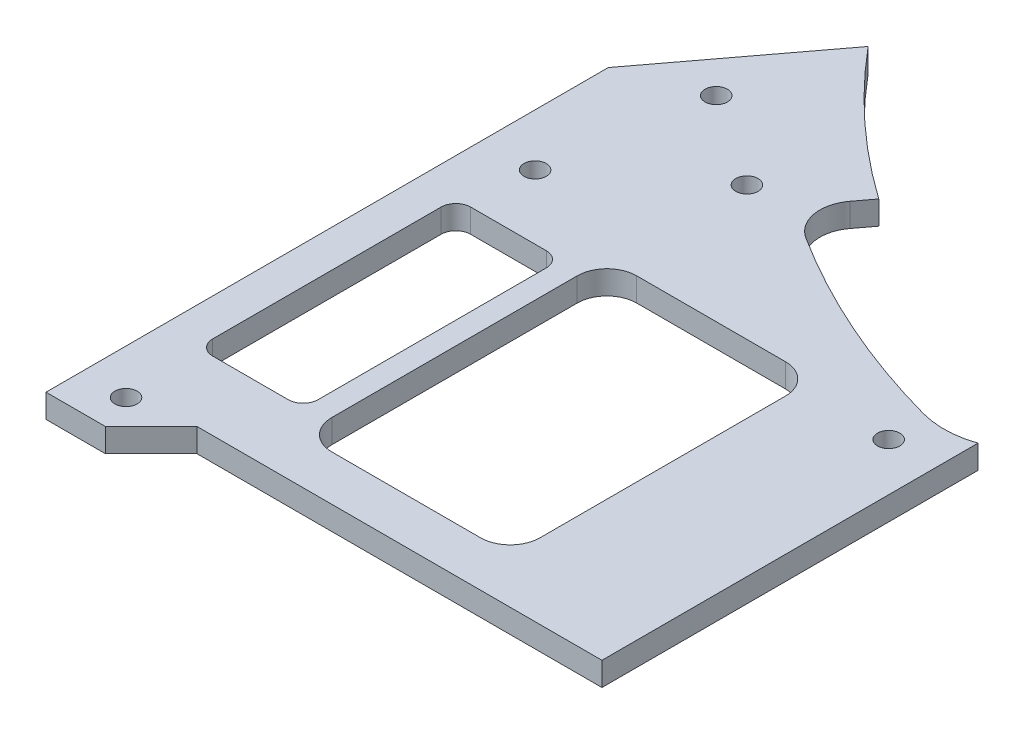
SolidWorks part; units mm, degrees
ref_plane "Front Plane" through (0, 0, 0) normal (0, 0, 1) x (1, 0, 0)
ref_plane "Top Plane" through (0, 0, 0) normal (0, 1, 0) x (1, 0, 0)
ref_plane "Right Plane" through (0, 0, 0) normal (1, 0, 0) x (0, 0, -1)
ref_plane "Plane1" through (0, 32.825, 0) normal (0, 1, 0) x (1, 0, 0)
sketch "Sketch1" plane through (0, 32.825, 0) normal (0, 1, 0) x (1, 0, 0)
  line L0 (0, -953.7581) -> (0, 49046.2419) construction
  line L2 (-21.4932, -33.5073) -> (-57.3512, -81.0925)
  line L3 (-12.5, -98.0505) -> (-12.5, -36.5164)
  line L4 (-70, -107.2534) -> (-84.16, -107.2534)
  line L5 (-70, -141.9466) -> (-70, -107.2534)
  line L6 (-84.16, -141.9466) -> (-70, -141.9466)
  line L7 (-84.16, -107.2534) -> (-84.16, -141.9466)
  line L8 (-70, -107.2534) -> (-84.16, -107.2534)
  line L9 (-70, -141.9466) -> (-70, -107.2534)
  line L10 (-84.16, -141.9466) -> (-70, -141.9466)
  line L11 (-84.16, -107.2534) -> (-84.16, -141.9466)
  line L12 (70, -107.2534) -> (70, -141.9466)
  line L13 (84.16, -107.2534) -> (70, -107.2534)
  line L14 (84.16, -141.9466) -> (84.16, -107.2534)
  line L15 (64.16, -189.6) -> (89.16, -164.6)
  line L16 (89.16, -164.6) -> (89.16, -81.7632)
  line L17 (89.16, -81.7632) -> (17.57, 13.2399)
  line L18 (-17.57, 13.2399) -> (-89.16, -81.7632)
  line L19 (-89.16, -81.7632) -> (-89.16, -164.6)
  line L20 (-89.16, -164.6) -> (-64.16, -189.6)
  line L21 (-64.16, -189.6) -> (64.16, -189.6)
  line L22 (64.16, -189.6) -> (89.16, -164.6) construction
  line L23 (89.16, -164.6) -> (89.16, -81.7632) construction
  line L24 (89.16, -81.7632) -> (17.57, 13.2399)
  line L25 (-17.57, 13.2399) -> (-89.16, -81.7632)
  line L26 (-89.16, -81.7632) -> (-89.16, -164.6) construction
  line L27 (-89.16, -164.6) -> (-64.16, -189.6) construction
  line L28 (-64.16, -189.6) -> (64.16, -189.6) construction
  line L29 (70, -141.9466) -> (84.16, -141.9466)
  line L30 (70, -107.2534) -> (70, -141.9466)
  line L31 (84.16, -107.2534) -> (70, -107.2534)
  line L32 (84.16, -141.9466) -> (84.16, -107.2534)
  line L33 (70, -141.9466) -> (84.16, -141.9466)
  line L34 (-21.4932, -33.5073) -> (-57.3512, -81.0925)
  line L35 (-12.5, -98.0505) -> (-12.5, -36.5164) construction
  line L36 (57.3512, -81.0925) -> (21.4932, -33.5073)
  line L37 (12.5, -36.5164) -> (12.5, -98.0505)
  line L38 (57.3512, -81.0925) -> (21.4932, -33.5073)
  line L39 (12.5, -36.5164) -> (12.5, -98.0505) construction
  line L44 (-89.16, -157.3574) -> (-81.1894, -157.3574)
  line L49 (-89.16, -81.7632) -> (-89.16, -157.3574)
  line L50 (89.16, -81.7632) -> (89.16, -157.3574)
  line L84 (-12.5, -36.5164) -> (-12.5, -89.3001)
  line L85 (12.5, -36.5164) -> (12.5, -89.3001)
  line L127 (-81.1894, -157.3574) -> (-75.0321, -151.2)
  line L128 (-75.0321, -151.2) -> (75.0321, -151.2)
  line L131 (-67.3373, -146.2) -> (0, -146.2) construction
  line L659 (-83.16, -152.6) -> (-83.16, -162.1147) construction
  line L660 (0, -1063.8231) -> (0, 48936.1769) construction
  line L661 (81.1894, -157.3574) -> (75.0321, -151.2)
  line L662 (89.16, -157.3574) -> (81.1894, -157.3574)
  circle A0 centre (0, -124.6) radius 7
  circle A1 centre (0, -124.6) radius 14 construction
  arc A3 (17.57, 13.2399) -> (-17.57, 13.2399) centre (0, 0) ccw
  arc A4 (17.57, 13.2399) -> (-17.57, 13.2399) centre (0, 0) ccw
  circle A5 centre (0, 0) radius 3.9
  circle A6 centre (0, 0) radius 3.9
  circle A7 centre (0, -28) radius 1.3
  circle A8 centre (0, -28) radius 1.3
  arc A11 (-57.3512, -81.0925) -> (-56.0366, -88.3236) centre (-53.358, -84.1016) ccw
  arc A12 (-56.0366, -88.3236) -> (-18.3785, -102.9728) centre (0, 0) ccw
  arc A13 (-18.3785, -102.9728) -> (-12.5, -98.0505) centre (-17.5, -98.0505) ccw
  arc A14 (-12.5, -36.5164) -> (-21.4932, -33.5073) centre (-17.5, -36.5164) ccw
  arc A15 (-57.3512, -81.0925) -> (-56.0366, -88.3236) centre (-53.358, -84.1016) ccw
  arc A16 (-56.0366, -88.3236) -> (-18.3785, -102.9728) centre (0, 0) ccw construction
  arc A17 (-18.3785, -102.9728) -> (-12.5, -98.0505) centre (-17.5, -98.0505) ccw construction
  arc A18 (-12.5, -36.5164) -> (-21.4932, -33.5073) centre (-17.5, -36.5164) ccw
  arc A19 (56.0366, -88.3236) -> (57.3512, -81.0925) centre (53.358, -84.1016) ccw
  arc A20 (18.3785, -102.9728) -> (56.0366, -88.3236) centre (0, 0) ccw
  arc A21 (12.5, -98.0505) -> (18.3785, -102.9728) centre (17.5, -98.0505) ccw
  arc A22 (21.4932, -33.5073) -> (12.5, -36.5164) centre (17.5, -36.5164) ccw
  arc A23 (56.0366, -88.3236) -> (57.3512, -81.0925) centre (53.358, -84.1016) ccw
  arc A24 (18.3785, -102.9728) -> (56.0366, -88.3236) centre (0, 0) ccw construction
  arc A25 (12.5, -98.0505) -> (18.3785, -102.9728) centre (17.5, -98.0505) ccw construction
  arc A26 (21.4932, -33.5073) -> (12.5, -36.5164) centre (17.5, -36.5164) ccw
  arc A47 (-56.0366, -88.3236) -> (-27.6749, -100.8725) centre (0, 0) ccw
  arc A48 (-12.5, -89.3001) -> (-27.6749, -100.8725) centre (-24.5, -89.3001) cw
  arc A49 (56.0366, -88.3236) -> (27.6749, -100.8725) centre (0, 0) cw
  arc A50 (12.5, -89.3001) -> (27.6749, -100.8725) centre (24.5, -89.3001) ccw
  circle A369 centre (-83.16, -152.6) radius 4.7574 construction
  circle A370 centre (-83.16, -152.6) radius 6 construction
  point P64 (-83.16, -157.3574)
  dimension "D8" = 14
  dimension "D11" = 12
  dimension "D9" = 5
  dimension "D10" = 45
  dimension "D1" = 0
  dimension "D2" = 0
  dimension "D3" = 0
  dimension "D4" = 0
  dimension "D5" = 0
  dimension "D6" = 0
  dimension "D7" = 0
extrude "Boss-Extrude1" add sketch "Sketch1" along normal up to vertex (3.175 mm away)
fillet "Fillet1" radius 2 8 edges at (84.16, 34.4125, 107.2534) (70, 34.4125, 107.2534) (70, 34.4125, 141.9466) (84.16, 34.4125, 141.9466) (-70, 34.4125, 141.9466) (-84.16, 34.4125, 141.9466) (-84.16, 34.4125, 107.2534) (-70, 34.4125, 107.2534)
sketch "Sketch2" plane through (0, 36, 0) normal (0, 1, 0) x (1, 0, 0)
  circle A1 centre (-62.0889, -184.6) radius 1.5
  circle A2 centre (-62.0889, -184.6) radius 1.5
  circle A3 centre (-27, -106.2222) radius 1.5
  circle A4 centre (-27, -106.2222) radius 1.5
  circle A5 centre (-83.16, -152.6) radius 1.5
  circle A6 centre (-83.16, -152.6) radius 1.5
  circle A7 centre (-78.6387, -77.7709) radius 1.5
  circle A8 centre (-78.6387, -77.7709) radius 1.5
  circle A9 centre (27, -106.2222) radius 1.5
  circle A10 centre (27, -106.2222) radius 1.5
  circle A11 centre (62.0889, -184.6) radius 1.5
  circle A12 centre (62.0889, -184.6) radius 1.5
  circle A13 centre (83.16, -162.1147) radius 1.5
  circle A14 centre (83.16, -162.1147) radius 1.5
  circle A15 centre (78.6387, -77.7709) radius 1.5
  circle A16 centre (78.6387, -77.7709) radius 1.5
  circle A17 centre (83.16, -152.6) radius 1.5
  circle A18 centre (83.16, -152.6) radius 1.5
  circle A19 centre (-83.16, -162.1147) radius 1.5
  circle A20 centre (-83.16, -162.1147) radius 1.5
  dimension "D1" = 0
  dimension "D2" = 0
  dimension "D3" = 0
  dimension "D4" = 0
  dimension "D5" = 0
  dimension "D6" = 0
  dimension "D7" = 0
  dimension "D8" = 0
  dimension "D9" = 0
  dimension "D10" = 0
extrude "Cut-Extrude1" cut sketch "Sketch2" against normal through all
sketch "Sketch5" plane through (0, 36, 0) normal (0, 1, 0) x (1, 0, 0)
  line L0 (-39, -104.1) -> (-39, -144.6) construction
  line L1 (-67, -104.1) -> (-39, -104.1)
  line L2 (-67, -104.1) -> (-67, -145.1)
  line L3 (-67, -145.1) -> (-39, -145.1)
  line L4 (-39, -104.1) -> (-39, -145.1)
  line L5 (-53, -145.1) -> (-53, -104.1) construction
  line L6 (-67, -124.6) -> (-39, -124.6) construction
  line L8 (0, -1107.7852) -> (0, 48892.2148) construction
  line L9 (67, -145.1) -> (39, -145.1)
  line L10 (39, -104.1) -> (39, -145.1)
  line L11 (67, -104.1) -> (39, -104.1)
  line L12 (67, -104.1) -> (67, -145.1)
  line L13 (-201109.722, -124.6) -> (248890.278, -124.6) construction
  point P516 (-53, -124.6)
extrude "Cut-Extrude3" cut sketch "Sketch5" against normal through all
fillet "Fillet2" radius 4 8 edges at (39, 34.4125, 145.1) (39, 34.4125, 104.1) (67, 34.4125, 104.1) (67, 34.4125, 145.1) (-39, 34.4125, 145.1) (-67, 34.4125, 145.1) (-39, 34.4125, 104.1) (-67, 34.4125, 104.1)
sketch "Sketch10" plane through (0, 36, 0) normal (0, 1, 0) x (1, 0, 0)
  circle A0 centre (0, 17) radius 1.5
  circle A1 centre (-14.7224, 8.5) radius 1.5
  circle A2 centre (14.7224, 8.5) radius 1.5
  circle A3 centre (0, -44.2583) radius 1.5
  circle A4 centre (0, -67.7786) radius 1.5
  circle A5 centre (0, -91.2988) radius 1.5
  circle A6 centre (0, 17) radius 1.3 construction
  circle A7 centre (14.7224, 8.5) radius 1.3 construction
  circle A8 centre (-14.7224, 8.5) radius 1.3 construction
  circle A9 centre (0, -44.2583) radius 1.3 construction
  circle A10 centre (0, -67.7786) radius 1.3 construction
  circle A11 centre (0, -91.2988) radius 1.3 construction
  dimension "D1" = 3
extrude "nose-guard-screw-holes" cut sketch "Sketch10" against normal through all
sketch "Sketch11" plane through (0, 36, 0) normal (0, 1, 0) x (1, 0, 0)
  circle A0 centre (0, -124.6) radius 20
  circle A1 centre (0, -124.6) radius 7 construction
  dimension "D1" = 40
extrude "Cut-Extrude4" cut sketch "Sketch11" against normal through all
sketch "Sketch12" plane through (0, 36, 0) normal (0, 1, 0) x (1, 0, 0)
  circle A1 centre (-82.16, -98.6) radius 1.5
  circle A2 centre (-82.16, -98.6) radius 1.5
  circle A3 centre (66.1717, -86.1119) radius 1.5
  circle A4 centre (66.1717, -86.1119) radius 1.5
  circle A5 centre (82.16, -98.6) radius 1.5
  circle A6 centre (82.16, -98.6) radius 1.5
  circle A7 centre (-66.1717, -86.1119) radius 1.5
  circle A8 centre (-66.1717, -86.1119) radius 1.5
  dimension "D1" = 0
  dimension "D2" = 0
  dimension "D3" = 0
  dimension "D4" = 0
extrude "Cut-Extrude5" cut sketch "Sketch12" against normal through all
sketch "Sketch13" plane through (0, 36, 0) normal (0, 1, 0) x (1, 0, 0)
  circle A0 centre (0, 0) radius 96.5505
extrude "Cut-Extrude6" cut sketch "Sketch13" against normal through all
sketch "Sketch14" plane through (0, 36, 0) normal (0, 1, 0) x (1, 0, 0)
  line L1 (271.9465, 84.0402) -> (-20.5762, 84.0402)
  line L2 (271.9465, 84.0402) -> (271.9465, -172.0482)
  line L3 (271.9465, -172.0482) -> (-20.5762, -172.0482)
  line L4 (-20.5762, 84.0402) -> (-20.5762, -172.0482)
  line L5 (125.6851, -172.0482) -> (125.6851, 84.0402) construction
  line L6 (271.9465, -44.004) -> (-20.5762, -44.004) construction
  point P16 (125.6851, -44.004)
extrude "Cut-Extrude7" cut sketch "Sketch14" against normal through all
